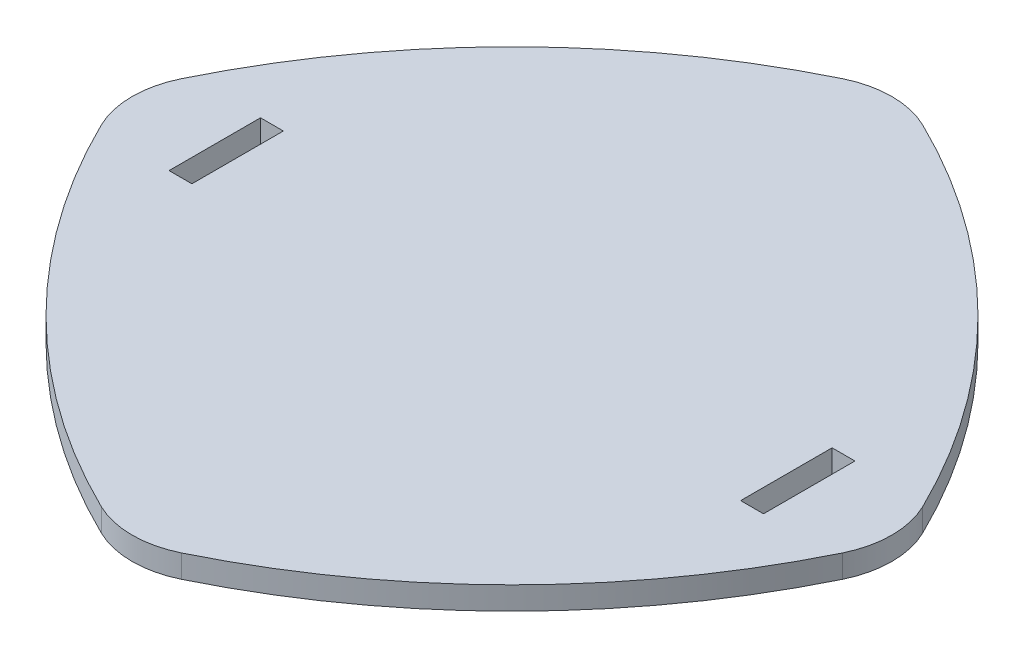
SolidWorks part; units mm, degrees
material "Acrylic (Medium-high impact)"
ref_plane "Front Plane" through (0, 0, 0) normal (0, 0, 1) x (1, 0, 0)
ref_plane "Top Plane" through (0, 0, 0) normal (0, 1, 0) x (1, 0, 0)
ref_plane "Right Plane" through (0, 0, 0) normal (1, 0, 0) x (0, 0, -1)
sketch "Sketch1" plane through (0, 0, 0) normal (0, 1, 0) x (1, 0, 0)
  circle A0 centre (0, 0) radius 8.5 construction
  arc A1 (-8.5, 0) -> (0, 8.5) centre (6.0104, -6.0104) cw
  arc A2 (0, 8.5) -> (8.5, 0) centre (-6.0104, -6.0104) cw
  arc A3 (8.5, 0) -> (0, -8.5) centre (-6.0104, 6.0104) cw
  arc A4 (0, -8.5) -> (-8.5, 0) centre (6.0104, 6.0104) cw
  point P18 (0, 0)
  dimension "D1" = 17
  dimension "D2" = 4
extrude "Boss-Extrude1" add sketch "Sketch1" along normal mid plane 0.5
fillet "Fillet1" radius 2 4 edges at (-8.5, 0, 0) (0, 0, -8.5) (8.5, 0, 0) (0, 0, 8.5)
sketch "Sketch2" plane through (0, 0.25, 0) normal (0, 1, 0) x (1, 0, 0)
  line L0 (-6.5, 0) -> (0, 0) construction
  line L1 (-6.5, -1) -> (-6, -1)
  line L2 (-6.5, -1) -> (-6.5, 1)
  line L3 (-6.5, 1) -> (-6, 1)
  line L4 (-6, -1) -> (-6, 1)
  line L5 (-6.5, -1) -> (-6, 1) construction
  line L6 (-6.5, 1) -> (-6, -1) construction
  line L7 (0, 0) -> (6.5, 0) construction
  line L9 (6, -1) -> (6.5, -1)
  line L10 (6, -1) -> (6, 1)
  line L11 (6, 1) -> (6.5, 1)
  line L12 (6.5, -1) -> (6.5, 1)
  line L13 (6, -1) -> (6.5, 1) construction
  line L14 (6, 1) -> (6.5, -1) construction
  point P0 (-6.25, 0)
  point P8 (6.25, 0)
  point P16 (0, 0)
  dimension "D1" = 2
  dimension "D2" = 0.5
  dimension "D3" = 6.5
extrude "Cut-Extrude1" cut sketch "Sketch2" against normal up to next
